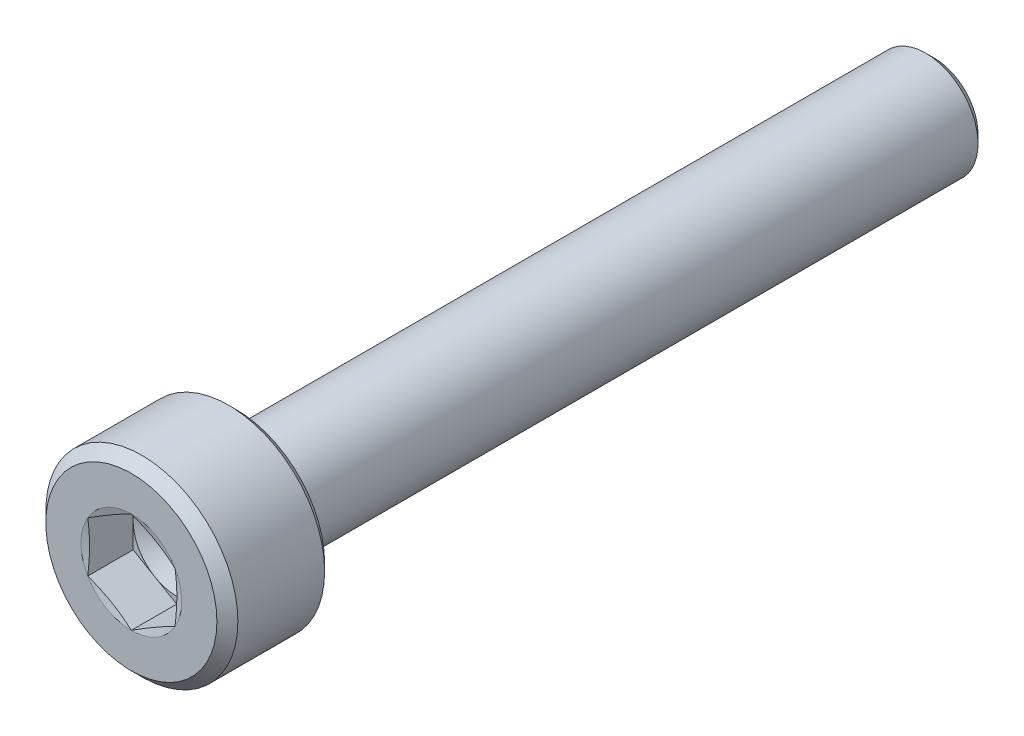
SolidWorks part; units mm, degrees
ref_plane "Front Plane" through (0, 0, 0) normal (0, 0, 1) x (1, 0, 0)
ref_plane "Top Plane" through (0, 0, 0) normal (0, 1, 0) x (1, 0, 0)
ref_plane "Right Plane" through (0, 0, 0) normal (1, 0, 0) x (0, 0, -1)
sketch "Sketch1" plane through (0, 0, 0) normal (1, 0, 0) x (0, 0, -1)
  line L0 (0, 0) -> (12.9407, 0) construction
  line L1 (0, 0) -> (0, 2.45)
  line L2 (0, 2.45) -> (0.3, 2.75)
  line L3 (0.3, 2.75) -> (2.785, 2.75)
  line L4 (3, 2.535) -> (3, 1.8)
  line L5 (3.51, 1.5) -> (22.75, 1.5)
  line L6 (22.75, 1.5) -> (23, 1.25)
  line L7 (23, 1.25) -> (23, 0)
  line L8 (23, 0) -> (0, 0)
  line L9 (2.785, 2.75) -> (3, 2.535)
  line L10 (3.4662, 1.5101) -> (3.0562, 1.7101)
  arc A2 (3.51, 1.5) -> (3.4662, 1.5101) centre (3.51, 1.6) cw
  arc A3 (3.0562, 1.7101) -> (3, 1.8) centre (3.1, 1.8) cw
  point P6 (3, 2.75)
  dimension "R2" = 0.1
  dimension "R1" = 0.1
  dimension "D1" = 45
  dimension "DK" = 5.5
  dimension "D3" = 45
  dimension "length" = 20
  dimension "K" = 3
  dimension "V" = 0.3
  dimension "HOLESIZE" = 3
  dimension "D4" = 2.5
  dimension "D5" = 45
  dimension "DW" = 5.07
  dimension "F" = 0.51
  dimension "DA" = 3.6
revolve "Revolve1" add sketch "Sketch1" angle 360 about L0
cosmetic thread "Cosmetic Thread1" parameters "D1"=18.5, "D2"=3
sketch "Sketch2" plane through (0, 0, 0) normal (0, 0, 1) x (1, 0, 0)
  line L0 (0, 0) -> (0, 1.4434) construction
  line L2 (0, 1.4434) -> (-1.25, 0.7217)
  line L3 (-1.25, 0.7217) -> (-1.25, -0.7217)
  line L4 (-1.25, -0.7217) -> (0, -1.4434)
  line L5 (0, -1.4434) -> (1.25, -0.7217)
  line L6 (1.25, -0.7217) -> (1.25, 0.7217)
  line L7 (1.25, 0.7217) -> (0, 1.4434)
  circle A0 centre (0, 0) radius 1.25 construction
  dimension "S" = 2.5
extrude "Cut-Extrude1" cut sketch "Sketch2" against normal blind 1.3
sketch "Sketch3" plane through (0, 0, 0) normal (1, 0, 0) x (0, 0, -1)
  line L0 (1.3, 0) -> (23, 0) construction
  line L1 (23, -1.25) -> (23, 1.25) construction
  line L2 (1.3, 0) -> (1.3, 1.25)
  line L4 (1.3, 1.25) -> (2.0217, 0)
  line L5 (2.0217, 0) -> (1.3, 0)
  line L6 (0, 2.45) -> (0, -2.45) construction
  dimension "DRILLANG" = 60
  dimension "DRILL DEPTH" = 1.3
  dimension "S2" = 2.5
revolve "Cut-Revolve2" cut sketch "Sketch3" angle 360 about L0
sketch "Sketch4" plane through (0, 0, 0) normal (1, 0, 0) x (0, 0, -1)
  line L0 (0, 0) -> (4.6121, 0) construction
  line L1 (0, 1.4434) -> (0, 1.25)
  line L2 (0, 2.45) -> (0, -2.45) construction
  line L3 (0, 1.25) -> (0.0518, 1.25)
  line L4 (0.0518, 1.25) -> (0, 1.4434)
  point P12 (0.0259, 1.25)
  dimension "D1" = 2.5
  dimension "D2" = 15
revolve "Cut-Revolve3" cut sketch "Sketch4" angle 360 about L0
